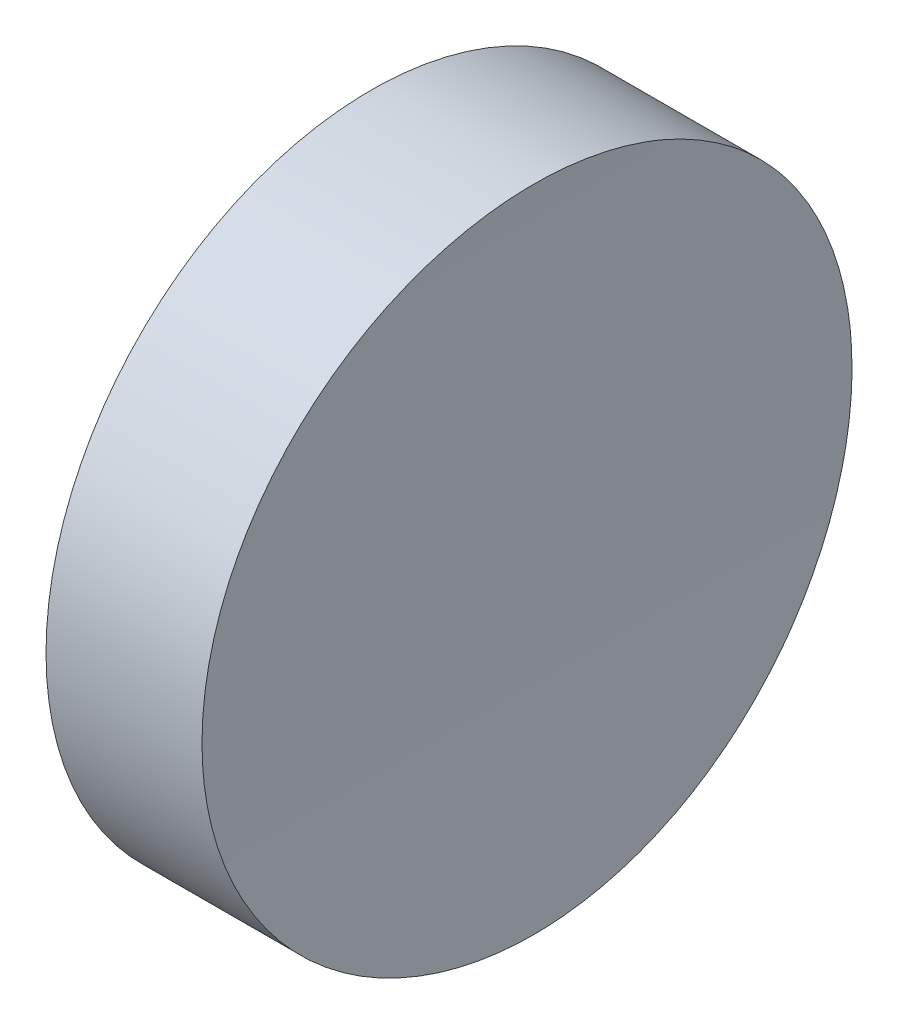
SolidWorks part; units mm, degrees
ref_plane "前视基准面" through (0, 0, 0) normal (0, 0, 1) x (1, 0, 0)
ref_plane "上视基准面" through (0, 0, 0) normal (0, 1, 0) x (1, 0, 0)
ref_plane "右视基准面" through (0, 0, 0) normal (1, 0, 0) x (0, 0, -1)
sketch "草图1" plane through (0, 0, 0) normal (1, 0, 0) x (0, 0, -1)
  circle A0 centre (0, 0) radius 6.25
  dimension "D1" = 12.5
extrude "凸台-拉伸1" add sketch "草图1" along normal blind 10
sketch "草图2" plane through (0, 0, 0) normal (0, 0, 1) x (1, 0, 0)
  line L0 (0, 0) -> (153, 0) construction
  line L1 (0, 0) -> (3, 0) construction
  circle A0 centre (153, 0) radius 150
  dimension "D1" = 300
  dimension "D2" = 3
extrude "切除-拉伸1" cut sketch "草图2" against normal through all both and the other way through all
